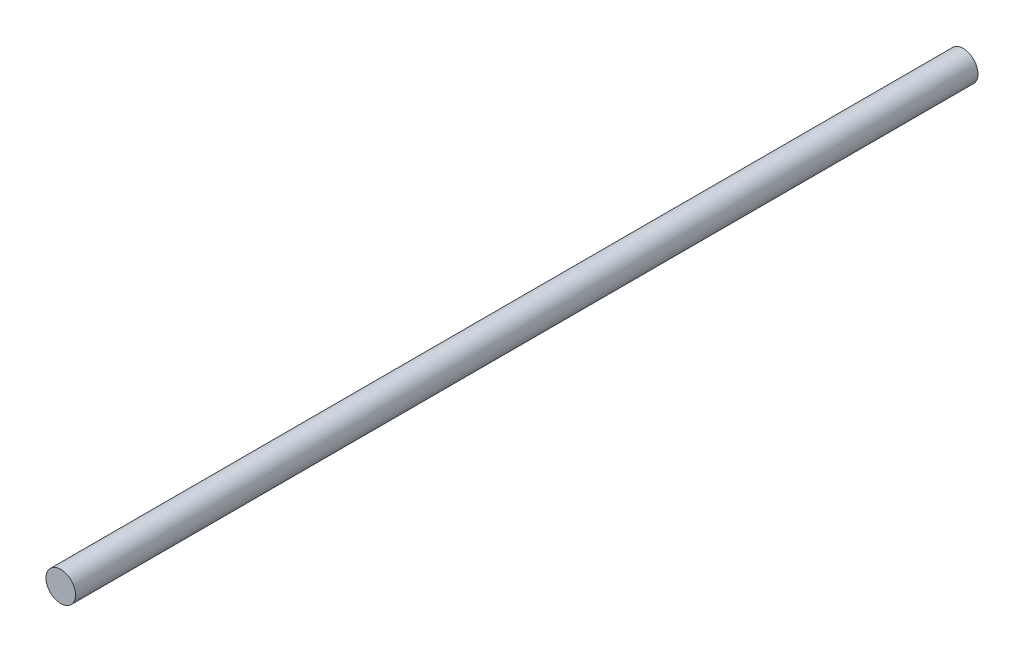
SolidWorks part; units mm, degrees
ref_plane "Front Plane" through (0, 0, 0) normal (0, 0, 1) x (1, 0, 0)
ref_plane "Top Plane" through (0, 0, 0) normal (0, 1, 0) x (1, 0, 0)
ref_plane "Right Plane" through (0, 0, 0) normal (1, 0, 0) x (0, 0, -1)
sketch "Sketch1" plane through (0, 0, 0) normal (0, 0, 1) x (1, 0, 0)
  circle A0 centre (0, 0) radius 12.7
  dimension "D1" = 25.4
extrude "Boss-Extrude1" add sketch "Sketch1" along normal blind 774.7
